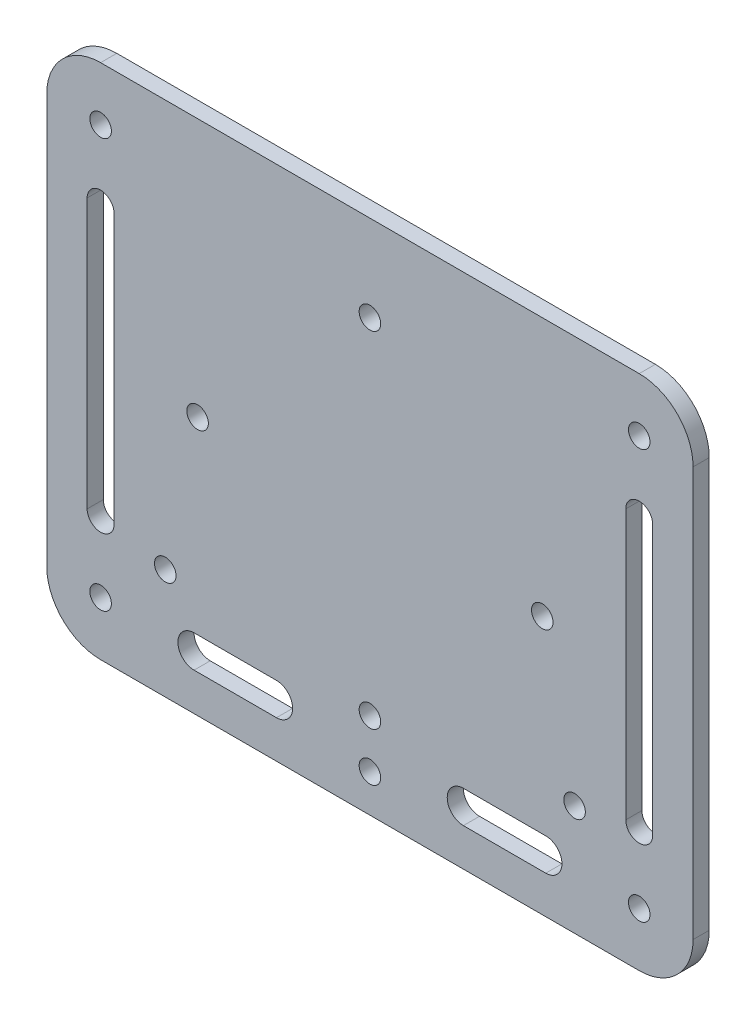
SolidWorks part; units mm, degrees
ref_plane "Front Plane" through (0, 0, 0) normal (0, 0, 1) x (1, 0, 0)
ref_plane "Top Plane" through (0, 0, 0) normal (0, 1, 0) x (1, 0, 0)
ref_plane "Right Plane" through (0, 0, 0) normal (1, 0, 0) x (0, 0, -1)
sketch "Sketch1" plane through (0, 0, 0) normal (0, 0, 1) x (1, 0, 0)
  line L0 (17.3519, -38) -> (32.6481, -38) construction
  line L1 (-50, 48) -> (50, 48)
  line L2 (-60, 38) -> (-60, -38)
  line L3 (-50, -48) -> (50, -48)
  line L4 (60, 38) -> (60, -38)
  line L5 (-60, 48) -> (-56.7373, 45.3898) construction
  line L6 (-60, -48) -> (-56.7373, -45.3898) construction
  line L11 (17.3519, -35) -> (32.6481, -35)
  line L12 (17.3519, -41) -> (32.6481, -41)
  line L18 (50, 25) -> (50, -25) construction
  line L19 (52.5, 25) -> (52.5, -25)
  line L20 (47.5, 25) -> (47.5, -25)
  line L21 (-32.6481, -38) -> (-17.3519, -38) construction
  line L25 (-50, 25) -> (-50, -25) construction
  line L26 (-47.5, 25) -> (-47.5, -25)
  line L27 (-52.5, 25) -> (-52.5, -25)
  line L28 (56.7373, -45.3898) -> (60, -48) construction
  line L29 (-32.6481, -35) -> (-17.3519, -35)
  line L30 (56.7373, 45.3898) -> (60, 48) construction
  line L31 (-32.6481, -41) -> (-17.3519, -41)
  circle A0 centre (0, 32) radius 2
  circle A1 centre (0, -32) radius 2
  circle A2 centre (32, 0) radius 2
  circle A3 centre (-32, 0) radius 2
  arc A4 (-50, 48) -> (-60, 38) centre (-50, 38) ccw
  arc A5 (-60, -38) -> (-50, -48) centre (-50, -38) ccw
  arc A6 (50, -48) -> (60, -38) centre (50, -38) ccw
  arc A7 (50, 48) -> (60, 38) centre (50, 38) cw
  arc A16 (52.5, 25) -> (47.5, 25) centre (50, 25) ccw
  arc A17 (47.5, -25) -> (52.5, -25) centre (50, -25) ccw
  arc A22 (-47.5, 25) -> (-52.5, 25) centre (-50, 25) ccw
  arc A23 (-52.5, -25) -> (-47.5, -25) centre (-50, -25) ccw
  circle A24 centre (-50, 38) radius 2
  circle A25 centre (50, 38) radius 2
  circle A26 centre (50, -38) radius 2
  circle A27 centre (-50, -38) radius 2
  circle A28 centre (-38, -27.5) radius 2
  circle A29 centre (38, -27.5) radius 2
  arc A30 (17.3519, -35) -> (17.3519, -41) centre (17.3519, -38) ccw
  arc A31 (32.6481, -41) -> (32.6481, -35) centre (32.6481, -38) ccw
  arc A32 (-32.6481, -35) -> (-32.6481, -41) centre (-32.6481, -38) ccw
  arc A33 (-17.3519, -41) -> (-17.3519, -35) centre (-17.3519, -38) ccw
  circle A34 centre (0, -41) radius 2
  point P0 (0, 0)
  point P27 (0, 0)
  point P40 (25, -38)
  point P48 (0, 0)
  point P51 (-50, 0)
  point P55 (50, 0)
  point P80 (-25, -38)
  dimension "D3" = 10
  dimension "D6" = 76
  dimension "D4" = 64
  dimension "D1" = 120
  dimension "D2" = 96
extrude "Boss-Extrude1" add sketch "Sketch1" along normal blind 3
